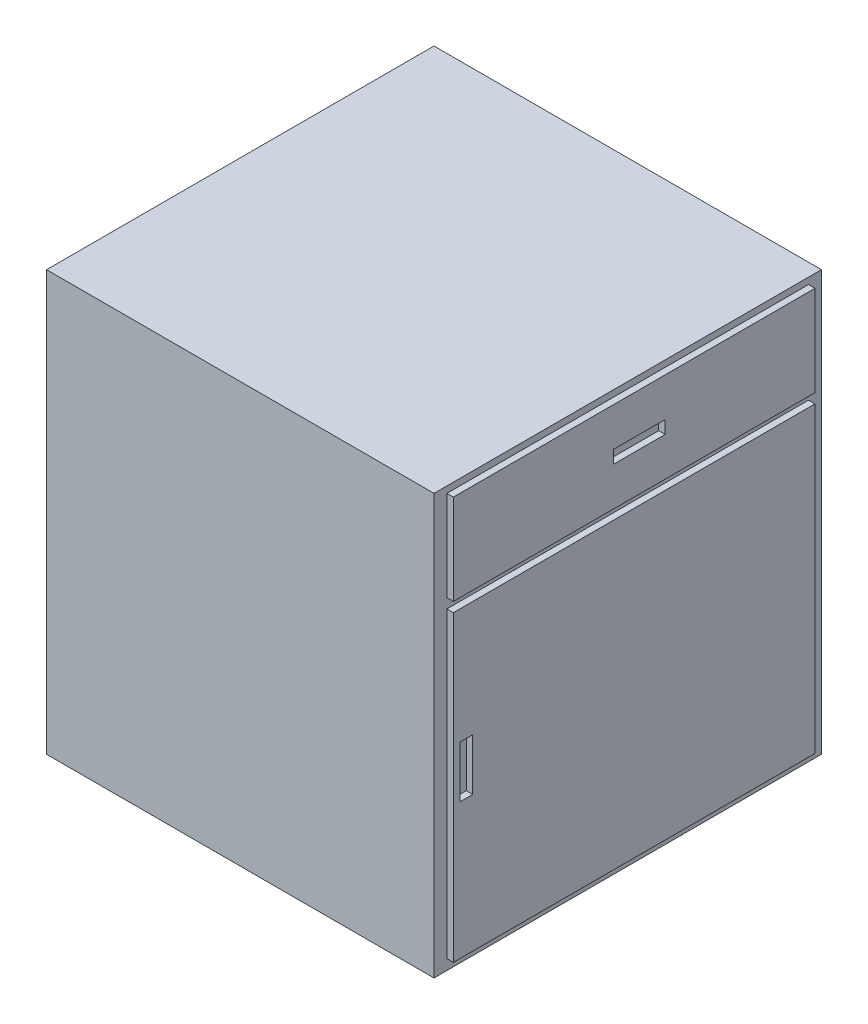
SolidWorks part; units mm, degrees
ref_plane "Front Plane" through (0, 0, 0) normal (0, 0, 1) x (1, 0, 0)
ref_plane "Top Plane" through (0, 0, 0) normal (0, 1, 0) x (1, 0, 0)
ref_plane "Right Plane" through (0, 0, 0) normal (1, 0, 0) x (0, 0, -1)
sketch "Sketch1" plane through (0, 0, 0) normal (0, 0, 1) x (1, 0, 0)
  line L1 (0, 0) -> (-600, 0)
  line L2 (0, 0) -> (0, -650)
  line L3 (0, -650) -> (-600, -650)
  line L4 (-600, 0) -> (-600, -650)
  dimension "D1" = 650
  dimension "D2" = 600
extrude "Boss-Extrude1" add sketch "Sketch1" along normal blind 600
sketch "Sketch2" plane through (0, 0, 0) normal (1, 0, 0) x (0, 0, -1)
  line L0 (0, -650) -> (0, 0) construction
  line L1 (-580, -9.9966) -> (-20, -9.9966)
  line L2 (-580, -9.9966) -> (-580, -149.9966)
  line L3 (-580, -149.9966) -> (-20, -149.9966)
  line L4 (-20, -9.9966) -> (-20, -149.9966)
  line L5 (-580, -164.9966) -> (-20, -164.9966)
  line L6 (-580, -164.9966) -> (-580, -633.9721)
  line L7 (-580, -633.9721) -> (-20, -633.9721)
  line L8 (-20, -164.9966) -> (-20, -633.9721)
  line L9 (-570, -343.759) -> (-550, -343.759)
  line L10 (-570, -343.759) -> (-570, -423.759)
  line L11 (-570, -423.759) -> (-550, -423.759)
  line L12 (-550, -343.759) -> (-550, -423.759)
  line L13 (-332, -69.9605) -> (-252, -69.9605)
  line L14 (-332, -69.9605) -> (-332, -89.9605)
  line L15 (-332, -89.9605) -> (-252, -89.9605)
  line L16 (-252, -69.9605) -> (-252, -89.9605)
  line L17 (-600, -650) -> (-600, 0) construction
  dimension "D1" = 140
  dimension "D2" = 15
  dimension "D3" = 20
  dimension "D4" = 80
  dimension "D5" = 248
  dimension "D6" = 20
  dimension "D7" = 20
  dimension "D8" = 20
  dimension "D9" = 80
  dimension "D10" = 10
extrude "Boss-Extrude2" add sketch "Sketch2" along normal blind 10
